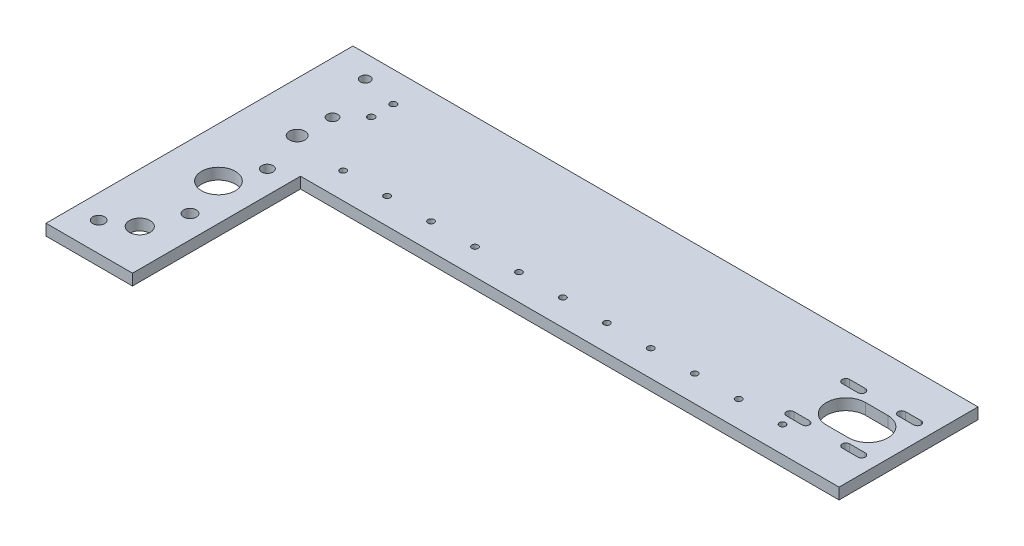
SolidWorks part; units mm, degrees
ref_plane "Front Plane" through (0, 0, 0) normal (0, 0, 1) x (1, 0, 0)
ref_plane "Top Plane" through (0, 0, 0) normal (0, 1, 0) x (1, 0, 0)
ref_plane "Right Plane" through (0, 0, 0) normal (1, 0, 0) x (0, 0, -1)
sketch "Sketch1" plane through (0, 0, 0) normal (0, 1, 0) x (1, 0, 0)
  line L0 (-198.1348, 0) -> (213.2351, 0) construction
  line L1 (0, -180.7465) -> (0, 169.7644) construction
  line L2 (-177.8, -87.3125) -> (-177.8, 87.3125)
  line L3 (-177.8, 87.3125) -> (177.8, 87.3125)
  line L4 (177.8, 87.3125) -> (177.8, 8.2677)
  line L5 (177.8, 8.2677) -> (-128.5875, 8.2677)
  line L6 (-128.5875, 8.2677) -> (-128.5875, -87.3125)
  line L7 (-128.5875, -87.3125) -> (-177.8, -87.3125)
  dimension "D1" = 355.6
  dimension "D2" = 177.8
  dimension "D3" = 174.625
  dimension "D4" = 87.3125
  dimension "D5" = 49.2125
  dimension "D6" = 79.0448
extrude "Boss-Extrude1" add sketch "Sketch1" along normal blind 6.35
sketch "Sketch2" plane through (0, 6.35, 0) normal (0, 1, 0) x (1, 0, 0)
  line L0 (-177.8, 87.3125) -> (-177.8, -87.3125) construction
  line L1 (143.6116, 35.2552) -> (156.3116, 35.2552)
  line L2 (127.7366, 60.1472) -> (136.6266, 60.1472)
  line L3 (159.4866, 30.4927) -> (127.7366, 30.4927) construction
  line L4 (159.4866, 30.4927) -> (159.4866, 62.2427) construction
  line L5 (159.4866, 62.2427) -> (127.7366, 62.2427) construction
  line L6 (127.7366, 30.4927) -> (127.7366, 62.2427) construction
  line L7 (159.4866, 30.4927) -> (127.7366, 62.2427) construction
  line L8 (159.4866, 62.2427) -> (127.7366, 30.4927) construction
  line L9 (136.6266, 64.3382) -> (127.7366, 64.3382)
  line L10 (-209.3283, 46.3677) -> (190.5302, 46.3677) construction
  line L11 (143.6116, 75.8016) -> (143.6116, 36.9062) construction
  line L12 (168.3766, 64.3382) -> (159.4866, 64.3382)
  line L13 (159.4866, 60.1472) -> (168.3766, 60.1472)
  line L14 (159.4866, 32.5882) -> (168.3766, 32.5882)
  line L15 (168.3766, 28.3972) -> (159.4866, 28.3972)
  line L16 (127.7366, 32.5882) -> (136.6266, 32.5882)
  line L17 (136.6266, 28.3972) -> (127.7366, 28.3972)
  line L18 (143.6116, 57.4802) -> (156.3116, 57.4802)
  line L19 (-128.5875, 8.2677) -> (177.8, 8.2677) construction
  line L20 (156.3116, 63.3203) -> (156.3116, 27.9055) construction
  arc A0 (127.7366, 64.3382) -> (127.7366, 60.1472) centre (127.7366, 62.2427) ccw
  arc A1 (136.6266, 60.1472) -> (136.6266, 64.3382) centre (136.6266, 62.2427) ccw
  arc A2 (159.4866, 64.3382) -> (159.4866, 60.1472) centre (159.4866, 62.2427) ccw
  arc A3 (168.3766, 60.1472) -> (168.3766, 64.3382) centre (168.3766, 62.2427) ccw
  arc A4 (168.3766, 32.5882) -> (168.3766, 28.3972) centre (168.3766, 30.4927) cw
  arc A5 (159.4866, 28.3972) -> (159.4866, 32.5882) centre (159.4866, 30.4927) cw
  arc A6 (136.6266, 32.5882) -> (136.6266, 28.3972) centre (136.6266, 30.4927) cw
  arc A7 (127.7366, 28.3972) -> (127.7366, 32.5882) centre (127.7366, 30.4927) cw
  arc A8 (143.6116, 57.4802) -> (143.6116, 35.2552) centre (143.6116, 46.3677) ccw
  arc A10 (156.3116, 35.2552) -> (156.3116, 57.4802) centre (156.3116, 46.3677) ccw
  circle A11 centre (-148.4884, 46.3677) radius 2.979
  point P5 (143.6116, 46.3677)
  dimension "D1" = 31.75
  dimension "D3" = 4.191
  dimension "D4" = 8.89
  dimension "D5" = 22.225
  dimension "D6" = 12.7
  dimension "D7" = 38.1
  dimension "D8" = 292.1
  dimension "D9" = 29.3116
  dimension "D2" = 2
extrude "Cut-Extrude1" cut sketch "Sketch2" against normal through all contours L1 A10 L18 A8 | L13 A3 L12 A2 | A5 L15 A4 L14 | L2 A1 L9 A0 | L17 A7 L16 A6 | A11
sketch "Sketch3" plane through (0, 6.35, 0) normal (0, 1, 0) x (1, 0, 0)
  line L0 (-149.5425, 98.7982) -> (-149.5425, -96.8969) construction
  line L1 (-183.7628, -17.4625) -> (-105.8972, -17.4625) construction
  line L2 (-177.8, -87.3125) -> (-128.5875, -87.3125) construction
  line L3 (-141.6304, 8.389) -> (-141.6304, -79.8315) construction
  line L4 (-128.5875, -87.3125) -> (-128.5875, 8.2677) construction
  circle A0 centre (-149.5425, 27.305) radius 4.4004
  circle A1 centre (-149.5425, -17.4625) radius 9.6044
  circle A2 centre (-149.5425, -62.23) radius 5.8666
  circle A3 centre (-141.6304, 2.4689) radius 3.2265
  circle A4 centre (-141.6304, -41.5361) radius 3.5959
  circle A5 centre (-164.3137, -70.8289) radius 3.3869
  circle A6 centre (-157.9987, 74.5127) radius 2.8179
  circle A7 centre (-137.7017, 70.1633) radius 1.8402
  circle A8 centre (-137.7017, 57.55) radius 1.931
  dimension "D1" = 44.7675
  dimension "D2" = 89.535
  dimension "D3" = 69.85
  dimension "D4" = 20.955
extrude "Cut-Extrude2" cut sketch "Sketch3" against normal through all
sketch "Sketch4" plane through (0, 6.35, 0) normal (0, 1, 0) x (1, 0, 0)
  line L0 (190.2841, 23.1267) -> (-208.8591, 23.1267) construction
  line L1 (177.8, 8.2677) -> (177.8, 87.3125) construction
  line L2 (-128.5875, 8.2677) -> (177.8, 8.2677) construction
  circle A0 centre (130.81, 23.1267) radius 1.778
  circle A22 centre (105.81, 23.1267) radius 1.778
  circle A23 centre (80.81, 23.1267) radius 1.778
  circle A24 centre (55.81, 23.1267) radius 1.778
  circle A25 centre (30.81, 23.1267) radius 1.778
  circle A26 centre (5.81, 23.1267) radius 1.778
  circle A27 centre (-19.19, 23.1267) radius 1.778
  circle A28 centre (-44.19, 23.1267) radius 1.778
  circle A29 centre (-69.19, 23.1267) radius 1.778
  circle A30 centre (-94.19, 23.1267) radius 1.778
  circle A31 centre (-119.19, 23.1267) radius 1.778
  dimension "D4" = 3.556
  dimension "D2" = 46.99
  dimension "D3" = 14.859
extrude "Cut-Extrude3" cut sketch "Sketch4" against normal through all
